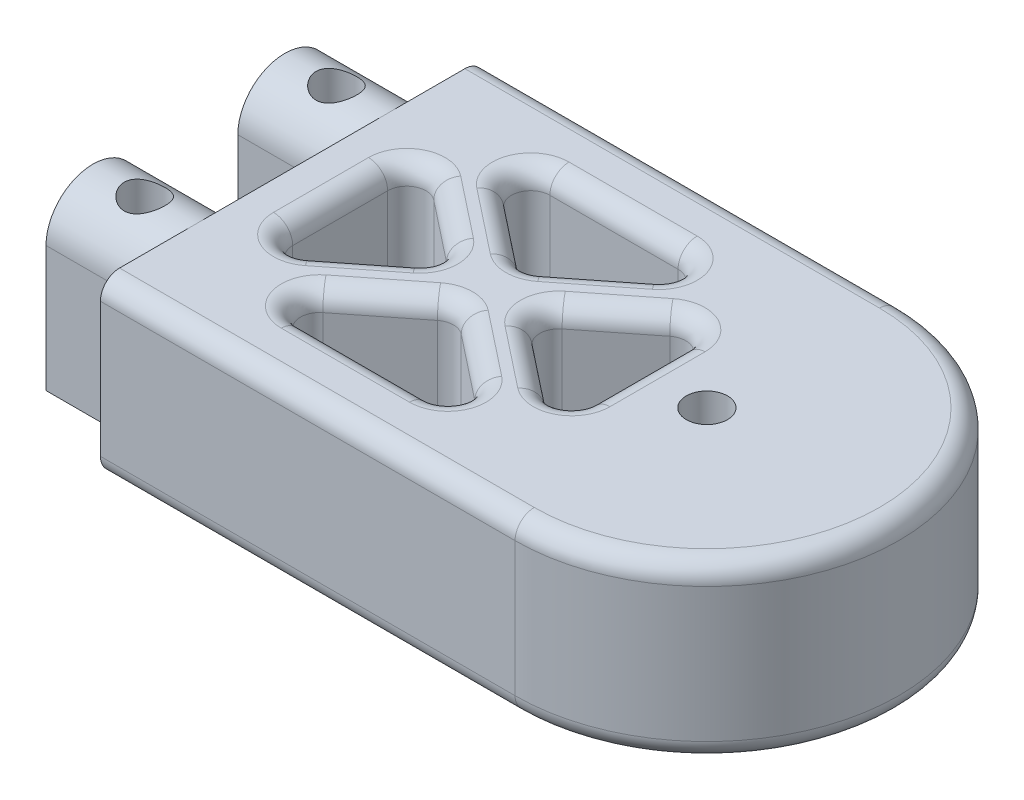
SolidWorks part; units mm, degrees
ref_plane "Front Plane" through (0, 0, 0) normal (0, 0, 1) x (1, 0, 0)
ref_plane "Top Plane" through (0, 0, 0) normal (0, 1, 0) x (1, 0, 0)
ref_plane "Right Plane" through (0, 0, 0) normal (1, 0, 0) x (0, 0, -1)
sketch "Sketch1" plane through (0, 0, 0) normal (1, 0, 0) x (0, 0, -1)
  line L0 (-20, -9) -> (20, -9)
  line L1 (-20, -9) -> (-20, 9)
  line L2 (-20, 9) -> (20, 9)
  line L3 (20, -9) -> (20, 9)
  line L4 (-20, -9) -> (20, 9) construction
  line L5 (-20, 9) -> (20, -9) construction
  point P0 (0, 0)
  dimension "D1" = 40
  dimension "D2" = 18
extrude "Boss-Extrude1" add sketch "Sketch1" along normal blind 63.235
sketch "Sketch2" plane through (0, 9, 0) normal (0, 1, 0) x (1, 0, 0)
  line L3 (43.235, -20) -> (63.235, -20)
  line L4 (63.235, -20) -> (63.235, 0)
  line L5 (63.235, -20) -> (0, -20) construction
  line L6 (63.235, 20) -> (63.235, -20) construction
  arc A0 (43.235, -20) -> (63.235, 0) centre (43.235, 0) ccw
  point P12 (63.235, 0)
extrude "Cut-Extrude1" cut sketch "Sketch2" against normal through all
ref_plane "Plane1" through (0, 0, 0) normal (0, 0, -1) x (-1, 0, 0)
mirror "Mirror1" about plane through (0, 0, 0) normal (0, 0, -1) of "Cut-Extrude1"
sketch "Sketch3" plane through (0, 9, 0) normal (0, 1, 0) x (1, 0, 0)
  circle A0 centre (43.235, 0) radius 2.15
  arc A3 (43.235, -20) -> (43.235, 20) centre (43.235, 0) ccw construction
  dimension "D1" = 4.3
extrude "Cut-Extrude2" cut sketch "Sketch3" against normal through all
fillet "Fillet1" radius 2 6 edges at (21.6175, 9, -20) (63.235, 9, 0) (21.6175, -9, -20) (63.235, -9, 0) (21.6175, 9, 20) (21.6175, -9, 20)
sketch "Sketch4" plane through (0, 0, 0) normal (-1, 0, 0) x (0, 0, 1)
  line L0 (-20, 0) -> (0, 0) construction
  line L1 (-20, -7) -> (-20, 7) construction
  line L2 (14.9, -9) -> (5.1, -9)
  line L3 (-14.9, -9) -> (-5.1, -9)
  line L4 (-14.9, -9) -> (-14.9, 4.1)
  line L6 (-5.1, -9) -> (-5.1, 4.1)
  line L7 (-14.9, -9) -> (-6.1308, 7.1066) construction
  line L8 (-13.8692, 7.1066) -> (-5.1, -9) construction
  line L9 (0, 9) -> (0, -9) construction
  line L10 (-18, 9) -> (18, 9) construction
  line L11 (18, -9) -> (-18, -9) construction
  line L12 (14.9, -9) -> (14.9, 4.1)
  line L13 (5.1, -9) -> (5.1, 4.1)
  arc A0 (-14.9, 4.1) -> (-5.1, 4.1) centre (-10, 4.1) cw
  arc A1 (14.9, 4.1) -> (5.1, 4.1) centre (10, 4.1) ccw
  point P5 (-10, 0)
  point P8 (-10, -9)
  point P19 (-10, 9)
  dimension "D1" = 9.8
extrude "Boss-Extrude2" add sketch "Sketch4" along normal blind 10.77
sketch "Sketch5" plane through (0, -9, 0) normal (0, -1, 0) x (1, 0, 0)
  line L0 (0, 5.1) -> (-10.77, 14.9) construction
  line L1 (-10.77, 5.1) -> (0, 14.9) construction
  line L2 (-10.77, 0) -> (0, 0) construction
  circle A0 centre (-5.385, 10) radius 2.125
  circle A1 centre (-5.385, -10) radius 2.125
  dimension "D1" = 4.25
extrude "Cut-Extrude3" cut sketch "Sketch5" against normal through all
sketch "Sketch6" plane through (0, 9, 0) normal (0, 1, 0) x (1, 0, 0)
  line L0 (0, 10) -> (0, -10) construction
  line L1 (5, -13) -> (36.085, -13) construction
  line L2 (5, -13) -> (5, 13) construction
  line L3 (5, 13) -> (36.085, 13) construction
  line L4 (36.085, -13) -> (36.085, 13) construction
  line L5 (43.235, 18) -> (0, 18) construction
  line L6 (0, 0) -> (43.235, 0) construction
  line L7 (5, 9.0741) -> (32.9887, -13) construction
  line L8 (8.0963, 13) -> (36.085, -9.0741) construction
  line L9 (5, 9.0741) -> (8.0963, 13) construction
  line L10 (36.085, -9.0741) -> (32.9887, -13) construction
  line L11 (5, -9.0741) -> (32.9887, 13) construction
  line L12 (8.0963, -13) -> (36.085, 9.0741) construction
  line L13 (36.085, 9.0741) -> (32.9887, 13) construction
  line L14 (5, -9.0741) -> (8.0963, -13) construction
  line L15 (8.0963, 13) -> (32.9887, 13)
  line L16 (36.085, 9.0741) -> (36.085, -9.0741)
  line L17 (32.9887, -13) -> (8.0963, -13)
  line L18 (5, 9.0741) -> (5, -9.0741)
  line L19 (8.0963, 13) -> (20.5425, 3.184)
  line L20 (20.5425, 3.184) -> (32.9887, 13)
  line L21 (5, -9.0741) -> (16.5054, 0)
  line L22 (16.5054, 0) -> (5, 9.0741)
  line L23 (8.0963, -13) -> (20.5425, -3.184)
  line L24 (20.5425, -3.184) -> (32.9887, -13)
  line L25 (36.085, 9.0741) -> (24.5796, 0)
  line L26 (24.5796, 0) -> (36.085, -9.0741)
  circle A0 centre (43.235, 0) radius 2.15 construction
  point P10 (5, 0)
  point P16 (41.085, 0)
  dimension "D1" = 5
  dimension "D2" = 5
  dimension "D3" = 5
  dimension "D4" = 5
  dimension "D5" = 5
extrude "Cut-Extrude4" cut sketch "Sketch6" against normal through all
fillet "Fillet3" radius 2 36 edges at (5, 9, 0) (10.7527, 9, -4.537) (14.3194, 9, -8.092) (20.5425, 9, -13) (14.3194, 9, 8.092) (26.7656, 9, 8.092) (30.3323, 9, 4.537) (30.3323, 9, -4.537) (10.7527, 9, 4.537) (26.7656, 9, -8.092) (20.5425, 9, 13) (36.085, 9, 0) (5, 0, -9.0741) (16.5054, 0, 0) (5, 0, 9.0741) (32.9887, 0, -13) (8.0963, 0, -13) (20.5425, 0, -3.184) (8.0963, 0, 13) (20.5425, 0, 3.184) (32.9887, 0, 13) (36.085, 0, -9.0741) (24.5796, 0, 0) (36.085, 0, 9.0741) (5, -9, 0) (10.7527, -9, -4.537) (20.5425, -9, -13) (26.7656, -9, -8.092) (14.3194, -9, 8.092) (26.7656, -9, 8.092) (30.3323, -9, -4.537) (36.085, -9, 0) (10.7527, -9, 4.537) (14.3194, -9, -8.092) (20.5425, -9, 13) (30.3323, -9, 4.537)
